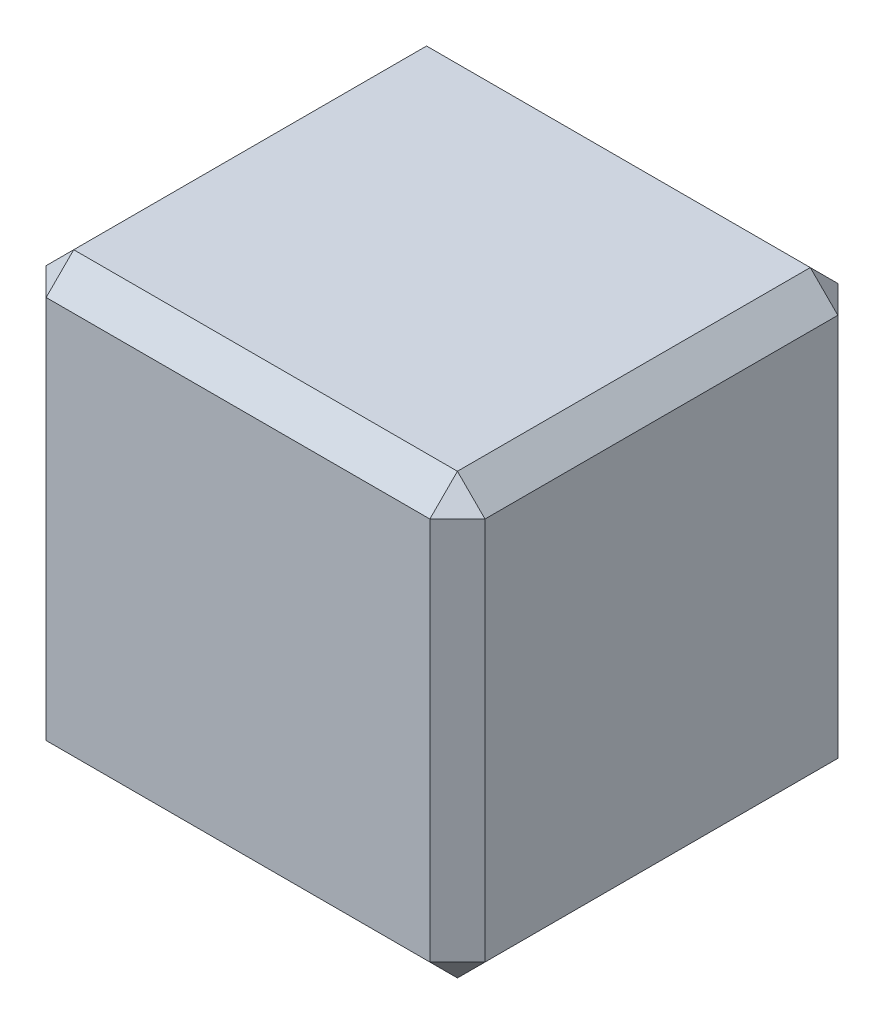
SolidWorks part; units mm, degrees
material "6061-T6 (SS)"
ref_plane "Front Plane" through (0, 0, 0) normal (0, 0, 1) x (1, 0, 0)
ref_plane "Top Plane" through (0, 0, 0) normal (0, 1, 0) x (1, 0, 0)
ref_plane "Right Plane" through (0, 0, 0) normal (1, 0, 0) x (0, 0, -1)
sketch "Sketch1" plane through (0, 0, 0) normal (0, 0, 1) x (1, 0, 0)
  line L1 (-12.6365, -12.6365) -> (12.6365, -12.6365)
  line L2 (-12.6365, -12.6365) -> (-12.6365, 12.6365)
  line L3 (-12.6365, 12.6365) -> (12.6365, 12.6365)
  line L4 (12.6365, -12.6365) -> (12.6365, 12.6365)
  line L5 (-12.6365, -12.6365) -> (12.6365, 12.6365) construction
  line L6 (-12.6365, 12.6365) -> (12.6365, -12.6365) construction
  point P0 (0, 0)
  dimension "D1" = 25.273
  dimension "D2" = 25.273
extrude "Boss-Extrude1" add sketch "Sketch1" along normal blind 23.495
chamfer "Chamfer2" distance 1.5875 angle 45 12 edges at (12.6365, 0, 0) (0, -12.6365, 0) (0, 12.6365, 0) (-12.6365, 0, 0) (0, -12.6365, 23.495) (12.6365, -12.6365, 11.7475) (12.6365, 0, 23.495) (-12.6365, 0, 23.495) (-12.6365, -12.6365, 11.7475) (12.6365, 12.6365, 11.7475) (0, 12.6365, 23.495) (-12.6365, 12.6365, 11.7475)
